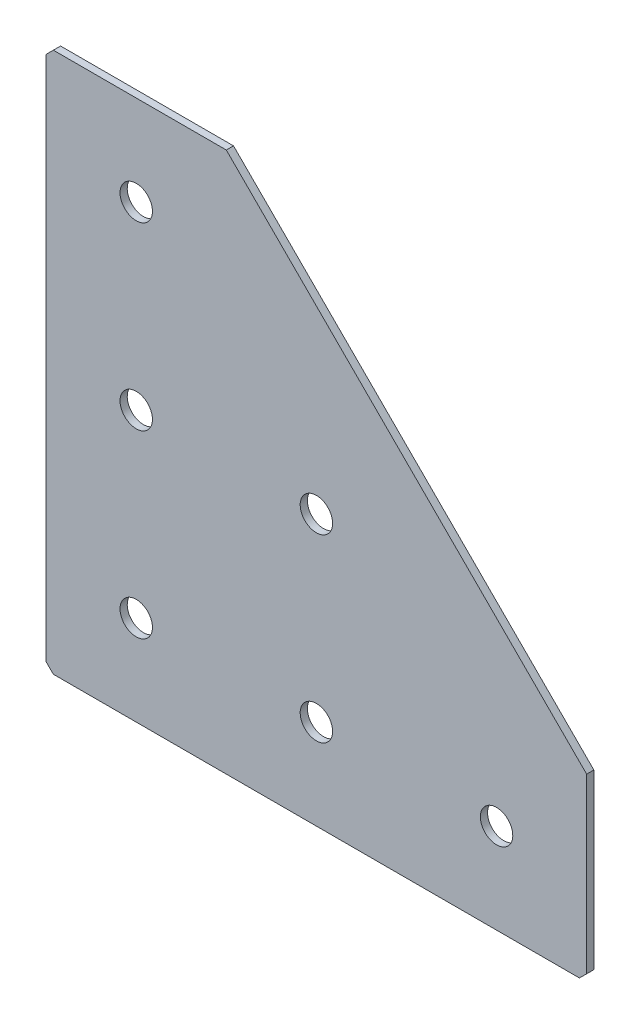
SolidWorks part; units mm, degrees
material "Простая углеродистая сталь"
ref_plane "Спереди(Плоскость XY)" through (0, 0, 0) normal (0, 0, 1) x (1, 0, 0)
ref_plane "Сверху(Плоскость XZ)" through (0, 0, 0) normal (0, 1, 0) x (1, 0, 0)
ref_plane "Справа(Плоскость ZY)" through (0, 0, 0) normal (1, 0, 0) x (0, 0, -1)
sketch "Эскиз1" plane through (0, 0, 0) normal (0, 0, -1) x (1, 0, 0)
  line L0 (0, 0) -> (0, 150)
  line L1 (0, 150) -> (150, 150)
  line L2 (150, 150) -> (150, 100)
  line L3 (150, 100) -> (50, 100) construction
  line L4 (50, 100) -> (50, 0) construction
  line L5 (50, 0) -> (0, 0)
  line L6 (150, 100) -> (50, 0)
  dimension "D1" = 150
  dimension "D3" = 50
extrude "Бобышка-Вытянуть1" add sketch "Эскиз1" along normal blind 2
hole_wizard "Отверстие с зазором M81" positions "Эскиз2" profile "Эскиз3" hole size "M8" standard "DIN" end condition through all
sketch "Эскиз2" plane through (0, 0, -2) normal (0, 0, -1) x (1, 0, 0)
  line L0 (25, 0) -> (25, 125) construction
  line L1 (0, 0) -> (50, 0) construction
  line L3 (150, 125) -> (0, 125) construction
  line L5 (0, 150) -> (0, 0) construction
  line L6 (150, 100) -> (150, 150) construction
  point P0 (75, 125)
  point P2 (25, 125)
  point P4 (25, 75)
  point P6 (25, 25)
  point P21 (125, 125)
  point P30 (75, 75)
  dimension "D1" = 50
  dimension "D2" = 50
  dimension "D3" = 50
  dimension "D4" = 25
  dimension "D5" = 50
sketch "Эскиз3" plane through (75, -125, -2) normal (1, 0, 0) x (0, 1, 0)
  line L0 (0, 0) -> (0, 2)
  line L1 (0, 2) -> (4.5, 2)
  line L2 (4.5, 2) -> (4.5, 0)
  line L5 (4.5, 0) -> (0, 0)
  line L11 (0, -6.35) -> (0, 107.95) construction
  dimension "Диаметр сквозного отверстия" = 9
  dimension "Глубина сквозного отверстия" = 2
chamfer "Фаска1" distance 2 angle 45 3 edges at (0, 0, -1) (150, -150, -1) (0, -150, -1)
